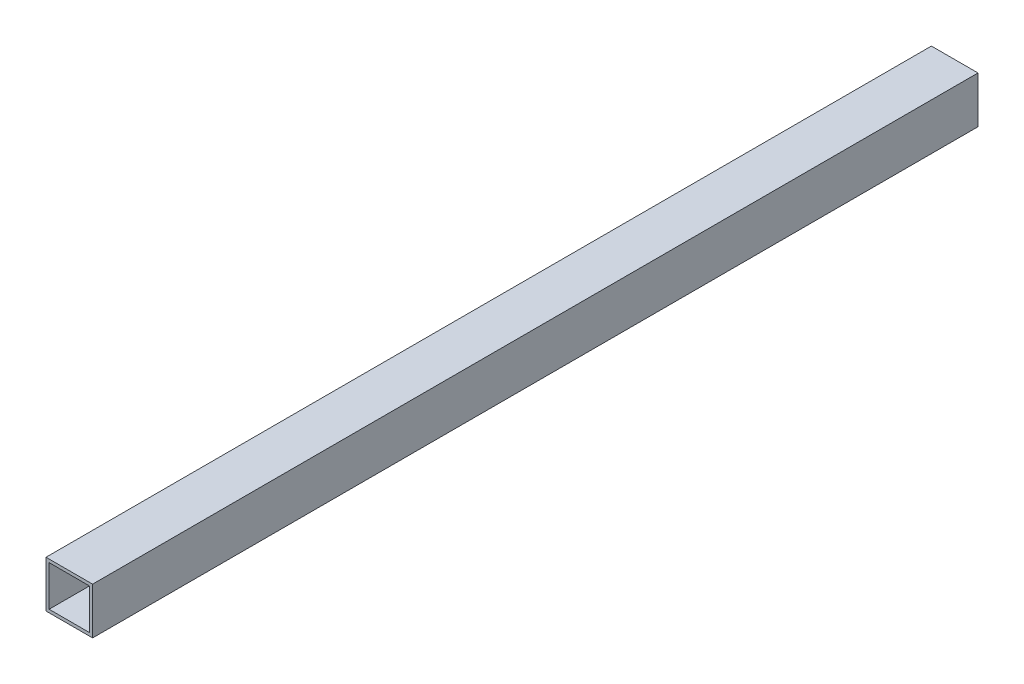
SolidWorks part; units mm, degrees
ref_plane "Front Plane" through (0, 0, 0) normal (0, 0, 1) x (1, 0, 0)
ref_plane "Top Plane" through (0, 0, 0) normal (0, 1, 0) x (1, 0, 0)
ref_plane "Right Plane" through (0, 0, 0) normal (1, 0, 0) x (0, 0, -1)
sketch "Esboço2" plane through (0, 0, 0) normal (0, 0, 1) x (1, 0, 0)
  line L1 (-94.2052, 59.6622) -> (-64.2052, 59.6622)
  line L2 (-94.2052, 59.6622) -> (-94.2052, 29.6622)
  line L3 (-94.2052, 29.6622) -> (-64.2052, 29.6622)
  line L4 (-64.2052, 59.6622) -> (-64.2052, 29.6622)
  dimension "D1" = 30
  dimension "D2" = 30
extrude "Ressalto-extrusão1" add sketch "Esboço2" along normal blind 570
shell "Casca2" thickness 2
